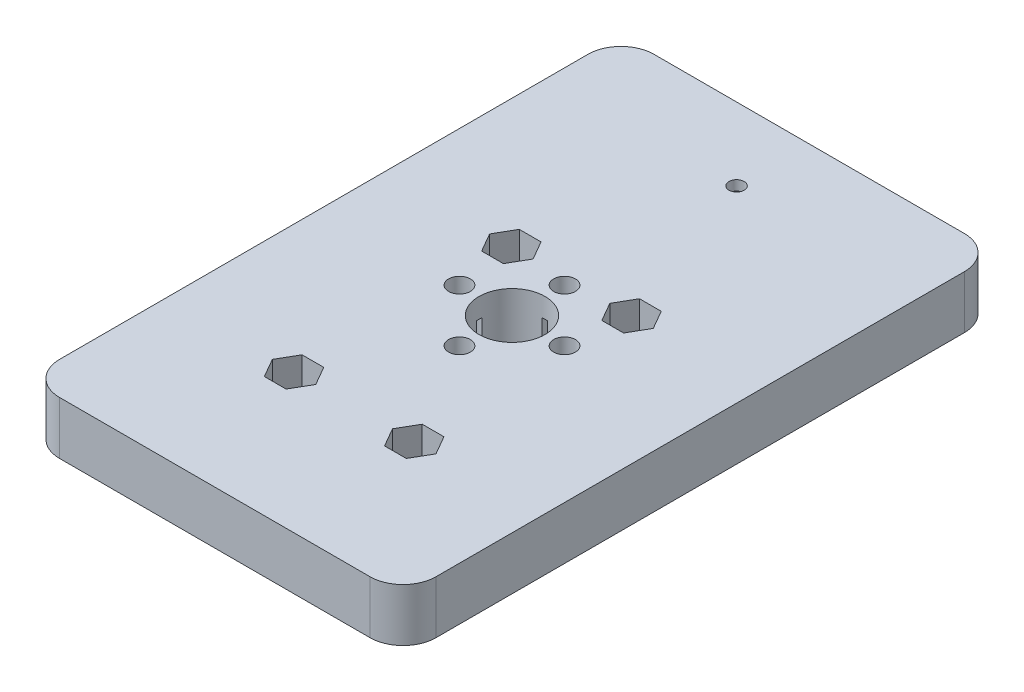
SolidWorks part; units mm, degrees
ref_plane "前视基准面" through (0, 0, 0) normal (0, 0, 1) x (1, 0, 0)
ref_plane "上视基准面" through (0, 0, 0) normal (0, 1, 0) x (1, 0, 0)
ref_plane "右视基准面" through (0, 0, 0) normal (1, 0, 0) x (0, 0, -1)
sketch "草图1" plane through (0, 0, 0) normal (0, 1, 0) x (1, 0, 0)
  line L0 (-7.955, 0) -> (0, 7.955) construction
  line L1 (-28.5, -45) -> (28.5, -45)
  line L2 (-28.5, -45) -> (-28.5, 45)
  line L3 (-28.5, 45) -> (28.5, 45)
  line L4 (28.5, -45) -> (28.5, 45)
  line L5 (-28.5, -45) -> (28.5, 45) construction
  line L6 (-28.5, 45) -> (28.5, -45) construction
  line L7 (-7.955, 0) -> (0, -7.955) construction
  line L8 (0, 7.955) -> (7.955, 0) construction
  line L9 (0, -7.955) -> (7.955, 0) construction
  line L10 (-7.955, 0) -> (7.955, 0) construction
  line L11 (0, 7.955) -> (0, -7.955) construction
  line L12 (-9.1, 9) -> (9.1, 9) construction
  line L13 (-9.1, 9) -> (-9.1, -23.9) construction
  line L14 (-9.1, -23.9) -> (9.1, -23.9) construction
  line L15 (9.1, 9) -> (9.1, -23.9) construction
  line L16 (-16, 14.87) -> (16, 14.87) construction
  line L17 (-16, 14.87) -> (-16, -31.13) construction
  line L18 (-16, -31.13) -> (16, -31.13) construction
  line L19 (16, 14.87) -> (16, -31.13) construction
  circle A1 centre (0, 0) radius 5
  circle A2 centre (0, 7.955) radius 1.65
  circle A3 centre (7.955, 0) radius 1.65
  circle A4 centre (0, -7.955) radius 1.65
  circle A5 centre (-7.955, 0) radius 1.65
  circle A6 centre (0, 0) radius 1.6182 construction
  circle A7 centre (9.1, 9) radius 1.65
  circle A8 centre (-9.1, 9) radius 1.65
  circle A9 centre (-9.1, -23.9) radius 1.65
  circle A10 centre (9.1, -23.9) radius 1.65
  point P0 (0, 0)
  point P24 (0, 14.87)
  point P25 (0, 9)
  point P40 (0, 0)
  dimension "D1" = 3.3
  dimension "D2" = 10
  dimension "D8" = 45
  dimension "D13" = 3.3
  dimension "D3" = 11.25
  dimension "D4" = 90
  dimension "D5" = 57
  dimension "D6" = 32.9
  dimension "D7" = 18.2
  dimension "D9" = 32
  dimension "D10" = 46
  dimension "D11" = 7.23
  dimension "D12" = 9
extrude "凸台-拉伸1" add sketch "草图1" along normal blind 8
sketch "草图2" plane through (0, 8, 0) normal (0, 1, 0) x (1, 0, 0)
  line L1 (-7.4546, 11.85) -> (-10.7454, 11.85)
  line L2 (-10.7454, 11.85) -> (-12.3909, 9)
  line L3 (-12.3909, 9) -> (-10.7454, 6.15)
  line L4 (-10.7454, 6.15) -> (-7.4546, 6.15)
  line L5 (-7.4546, 6.15) -> (-5.8091, 9)
  line L6 (-5.8091, 9) -> (-7.4546, 11.85)
  line L7 (10.7454, 11.85) -> (7.4546, 11.85)
  line L8 (7.4546, 11.85) -> (5.8091, 9)
  line L9 (5.8091, 9) -> (7.4546, 6.15)
  line L10 (7.4546, 6.15) -> (10.7454, 6.15)
  line L11 (10.7454, 6.15) -> (12.3909, 9)
  line L12 (12.3909, 9) -> (10.7454, 11.85)
  line L13 (10.7454, -21.05) -> (7.4546, -21.05)
  line L14 (7.4546, -21.05) -> (5.8091, -23.9)
  line L15 (5.8091, -23.9) -> (7.4546, -26.75)
  line L16 (7.4546, -26.75) -> (10.7454, -26.75)
  line L17 (10.7454, -26.75) -> (12.3909, -23.9)
  line L18 (12.3909, -23.9) -> (10.7454, -21.05)
  line L19 (-10.7454, -21.05) -> (-12.3909, -23.9)
  line L20 (-12.3909, -23.9) -> (-10.7454, -26.75)
  line L21 (-10.7454, -26.75) -> (-7.4546, -26.75)
  line L22 (-7.4546, -26.75) -> (-5.8091, -23.9)
  line L23 (-5.8091, -23.9) -> (-7.4546, -21.05)
  line L24 (-7.4546, -21.05) -> (-10.7454, -21.05)
  circle A4 centre (-9.1, 9) radius 2.85 construction
  circle A5 centre (9.1, 9) radius 2.85 construction
  circle A6 centre (9.1, -23.9) radius 2.85 construction
  circle A7 centre (-9.1, -23.9) radius 2.85 construction
  dimension "D1" = 5.7
extrude "切除-拉伸1" cut sketch "草图2" against normal offset from surface (5 mm away) 3 up to face at (-9.1, 0, 25.55)
sketch "草图3" plane through (0, 0, 0) normal (0, -1, 0) x (1, 0, 0)
  circle A0 centre (0, 7.955) radius 3
  circle A1 centre (7.955, 0) radius 3
  circle A2 centre (0, -7.955) radius 3
  circle A3 centre (-7.955, 0) radius 3
  dimension "D1" = 6
extrude "切除-拉伸2" cut sketch "草图3" against normal offset from surface (5 mm away) 3 up to face at (-9.1, 8, 23.9)
fillet "圆角1" radius 5 4 edges at (-28.5, 4, -45) (28.5, 4, -45) (28.5, 4, 45) (-28.5, 4, 45)
sketch "草图4" plane through (0, 8, 0) normal (0, 1, 0) x (1, 0, 0)
  circle A0 centre (0, 34) radius 1.15
  point P2 (0, 0)
  dimension "D1" = 2.3
  dimension "D2" = 34
extrude "切除-拉伸3" cut sketch "草图4" against normal through all
sketch "草图5" plane through (0, 0, 0) normal (0, -1, 0) x (1, 0, 0)
  circle A0 centre (0, -34) radius 2.15
  dimension "D1" = 4.3
extrude "切除-拉伸4" cut sketch "草图5" against normal offset from surface (6.5 mm away) 1.5 up to face at (0, 8, -32.85)
